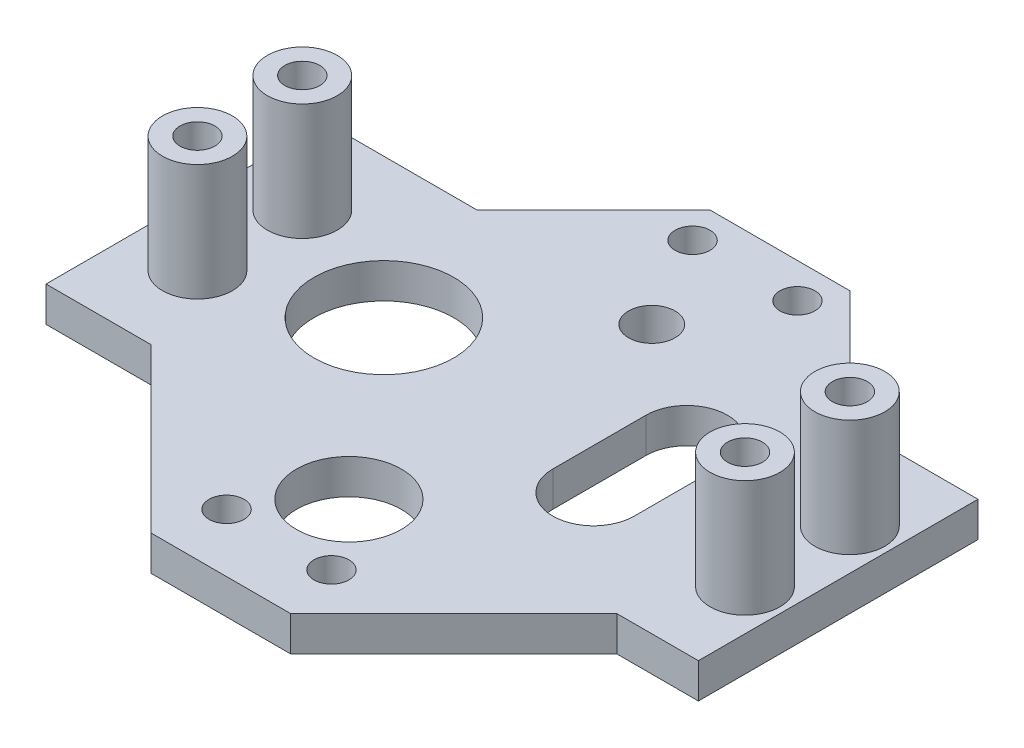
SolidWorks part; units mm, degrees
ref_plane "Front Plane" through (0, 0, 0) normal (0, 0, 1) x (1, 0, 0)
ref_plane "Top Plane" through (0, 0, 0) normal (0, 1, 0) x (1, 0, 0)
ref_plane "Right Plane" through (0, 0, 0) normal (1, 0, 0) x (0, 0, -1)
sketch "Sketch1" plane through (0, 0, 0) normal (0, 1, 0) x (1, 0, 0)
  line L0 (0, 48) -> (-10, 38)
  line L1 (0, 0) -> (12, 0)
  line L2 (0, 0) -> (0, 48)
  line L3 (0, 48) -> (12, 48)
  line L4 (12, 0) -> (12, 48)
  line L5 (-23, 38) -> (33, 38)
  line L6 (-23, 38) -> (-23, 14)
  line L7 (-23, 14) -> (33, 14)
  line L8 (33, 38) -> (33, 14)
  line L9 (12, 48) -> (22, 38)
  line L10 (0, 0) -> (-14, 14)
  line L11 (12, 0) -> (26, 14)
  dimension "D1" = 12
  dimension "D2" = 48
  dimension "D3" = 24
  dimension "D4" = 56
  dimension "D5" = 23
  dimension "D6" = 45
  dimension "D7" = 45
  dimension "D8" = 45
  dimension "D9" = 45
  dimension "D10" = 7
extrude "Boss-Extrude1" add sketch "Sketch1" along normal blind 3 contours L10 L2 L7 | L6 L7 L2 L5 | L9 L4 L5 | L2 L5 L4 L3 | L2 L7 L4 L5 | L8 L5 L4 L7 | L4 L11 L7 | L7 L2 L1 L4 | L0 L5 L2
sketch "Sketch2" plane through (0, 3, 0) normal (0, 1, 0) x (1, 0, 0)
  line L0 (0, 0) -> (12, 0) construction
  line L1 (1.5, 45) -> (10.5, 45)
  line L2 (1.5, 45) -> (1.5, 5)
  line L3 (1.5, 5) -> (10.5, 5)
  line L4 (10.5, 45) -> (10.5, 5)
  line L5 (0, 48) -> (12, 48) construction
  line L6 (6, 48) -> (6, 0) construction
  circle A0 centre (1.5, 45) radius 1.5
  circle A1 centre (10.5, 45) radius 1.5
  circle A2 centre (10.5, 5) radius 1.5
  circle A3 centre (1.5, 5) radius 1.5
  circle A4 centre (6, 37) radius 2
  circle A5 centre (6, 11) radius 4.5
  dimension "D5" = 3
  dimension "D6" = 3
  dimension "D7" = 3
  dimension "D8" = 3
  dimension "D9" = 4
  dimension "D10" = 9
  dimension "D1" = 9
  dimension "D2" = 3
  dimension "D3" = 5
  dimension "D4" = 4.5
  dimension "D11" = 11
  dimension "D12" = 11
extrude "Cut-Extrude1" cut sketch "Sketch2" against normal blind 3 contours L6 A4 | A4 L6 | L4 A1 L1 | L1 A1 L4 | L2 A0 L1 | L1 A0 L2 | A5 L6 | L6 A5 | L3 A3 L2 | L4 A2 L3 | L3 A2 L4 | L2 A3 L3
sketch "Sketch3" plane through (0, 3, 0) normal (0, 1, 0) x (1, 0, 0)
  line L0 (6, 48) -> (6, 0) construction
  line L1 (-17.5, 30.5) -> (29.5, 30.5) construction
  line L2 (-17.5, 30.5) -> (-17.5, 21.5) construction
  line L3 (-17.5, 21.5) -> (29.5, 21.5) construction
  line L4 (29.5, 30.5) -> (29.5, 21.5) construction
  line L5 (0, 48) -> (12, 48) construction
  line L6 (0, 0) -> (12, 0) construction
  line L7 (-23, 26) -> (33, 26) construction
  line L8 (-23, 38) -> (-23, 14) construction
  line L9 (33, 38) -> (33, 14) construction
  circle A0 centre (-17.5, 30.5) radius 3
  circle A1 centre (-17.5, 21.5) radius 3
  circle A2 centre (29.5, 30.5) radius 3
  circle A3 centre (29.5, 21.5) radius 3
  point P16 (-17.5, 26)
  point P17 (6, 30.5)
  dimension "D3" = 6
  dimension "D4" = 6
  dimension "D5" = 6
  dimension "D6" = 6
  dimension "D1" = 9
  dimension "D2" = 47
extrude "Boss-Extrude2" add sketch "Sketch3" along normal blind 10
sketch "Sketch4" plane through (0, 3, 0) normal (0, 1, 0) x (1, 0, 0)
  line L0 (33, 26) -> (-23, 26) construction
  line L1 (33, 38) -> (33, 14) construction
  line L2 (-23, 38) -> (-23, 14) construction
  line L3 (16, 22) -> (16, 30) construction
  line L4 (12.5, 22) -> (12.5, 30)
  line L5 (19.5, 22) -> (19.5, 30)
  circle A0 centre (23, 26) radius 1.5
  arc A1 (12.5, 22) -> (19.5, 22) centre (16, 22) ccw
  arc A2 (19.5, 30) -> (12.5, 30) centre (16, 30) ccw
  circle A3 centre (-6, 26) radius 6
  point P10 (16, 26)
  point P17 (16, 18.5)
  point P18 (16, 33.5)
  dimension "D4" = 3
  dimension "D7" = 12
  dimension "D1" = 10
  dimension "D2" = 17
  dimension "D3" = 17
  dimension "D5" = 7
  dimension "D6" = 15
extrude "Cut-Extrude2" cut sketch "Sketch4" against normal through all
sketch "Sketch5" plane through (0, 13, 0) normal (0, 1, 0) x (1, 0, 0)
  circle A1 centre (29.5, 30.5) radius 1.5
  circle A2 centre (29.5, 21.5) radius 1.5
  circle A3 centre (-17.5, 30.5) radius 1.5
  circle A4 centre (-17.5, 21.5) radius 1.5
  dimension "D1" = 3
  dimension "D2" = 3
  dimension "D3" = 3
  dimension "D4" = 3
extrude "Cut-Extrude3" cut sketch "Sketch5" against normal up to surface (10 mm away) up to face at (23, 3, -24.5)
